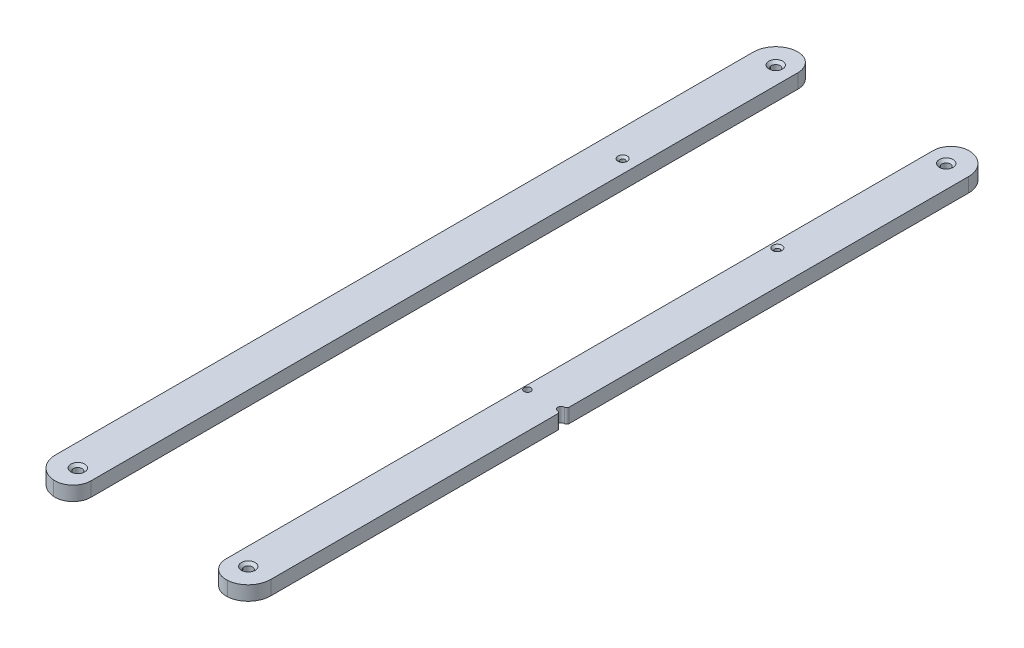
SolidWorks part; units mm, degrees
material "Acrylic (Medium-high impact)"
ref_plane "Front Plane" through (0, 0, 0) normal (0, 0, 1) x (1, 0, 0)
ref_plane "Top Plane" through (0, 0, 0) normal (0, 1, 0) x (1, 0, 0)
ref_plane "Right Plane" through (0, 0, 0) normal (1, 0, 0) x (0, 0, -1)
sketch "Sketch1" plane through (0, 0, 0) normal (0, 1, 0) x (1, 0, 0)
  line L0 (92.5, -137.5) -> (138.3433, -137.5)
  line L1 (148.3433, -127.5) -> (148.3433, 147.5)
  line L2 (158.3433, 157.5) -> (171.8825, 157.5)
  line L3 (181.8825, 167.5) -> (181.8825, 196.879)
  line L4 (171.8825, 206.879) -> (-36.0392, 206.879)
  line L5 (-46.0392, 92.5) -> (-46.0392, 196.879)
  line L6 (-51.0392, 87.5) -> (-77.5, 87.5)
  line L7 (-82.5, 82.5) -> (-82.5, 5)
  line L8 (-77.5, 0) -> (-57.5, 0)
  line L9 (-52.5, -5) -> (-52.5, -162.5)
  line L10 (-47.5, -167.5) -> (72.5, -167.5)
  line L11 (82.5, -157.5) -> (82.5, -147.5)
  line L12 (138.4217, -124.0875) -> (140.4217, -124.0875)
  line L13 (140.4217, -120.9125) -> (138.4217, -120.9125)
  line L14 (138.4217, 23.102) -> (140.4217, 23.102)
  line L15 (140.4217, 26.277) -> (138.4217, 26.277)
  arc A0 (138.3433, -137.5) -> (148.3433, -127.5) centre (138.3433, -127.5) ccw
  arc A1 (158.3433, 157.5) -> (148.3433, 147.5) centre (158.3433, 147.5) ccw
  arc A2 (171.8825, 157.5) -> (181.8825, 167.5) centre (171.8825, 167.5) ccw
  arc A3 (181.8825, 196.879) -> (171.8825, 206.879) centre (171.8825, 196.879) ccw
  arc A4 (-36.0392, 206.879) -> (-46.0392, 196.879) centre (-36.0392, 196.879) ccw
  arc A5 (-51.0392, 87.5) -> (-46.0392, 92.5) centre (-51.0392, 92.5) ccw
  arc A6 (-77.5, 87.5) -> (-82.5, 82.5) centre (-77.5, 82.5) ccw
  arc A7 (-82.5, 5) -> (-77.5, 0) centre (-77.5, 5) ccw
  arc A8 (-52.5, -5) -> (-57.5, 0) centre (-57.5, -5) ccw
  arc A9 (-52.5, -162.5) -> (-47.5, -167.5) centre (-47.5, -162.5) ccw
  arc A10 (72.5, -167.5) -> (82.5, -157.5) centre (72.5, -157.5) ccw
  arc A11 (92.5, -137.5) -> (82.5, -147.5) centre (92.5, -147.5) ccw
  circle A12 centre (67.5, 122.5) radius 1.7
  circle A13 centre (67.5, 82.5) radius 1.7
  circle A14 centre (67.5, 102.5) radius 1.7
  circle A15 centre (37.5, 82.5) radius 1.7
  circle A16 centre (67.5, 147.5) radius 1.7
  circle A17 centre (-32.5, 122.5) radius 1.7
  circle A18 centre (-2.5, 122.5) radius 1.7
  circle A19 centre (37.5, 122.5) radius 1.7
  circle A20 centre (37.5, 102.5) radius 1.7
  circle A21 centre (-32.5, 147.5) radius 1.7
  circle A22 centre (47.4217, 154.379) radius 1.75
  circle A23 centre (47.4217, 146.879) radius 1.5
  circle A24 centre (47.4217, 139.379) radius 1.75
  circle A25 centre (-6.5783, 139.379) radius 1.75
  circle A26 centre (-6.5783, 146.879) radius 1.5
  circle A27 centre (-6.5783, 154.379) radius 1.75
  circle A28 centre (-15.9636, -158.3264) radius 1.4732
  circle A29 centre (44.1717, 16.2044) radius 1.7272
  circle A30 centre (29.1717, 36.5) radius 1.7272
  circle A31 centre (29.1717, 18.5) radius 1.7272
  circle A32 centre (52.0479, 6.6629) radius 1.4732
  circle A33 centre (44.1717, 27.5) radius 1.5
  circle A34 centre (44.1717, 38.7956) radius 1.7272
  circle A35 centre (52.207, 48.3264) radius 1.4732
  circle A36 centre (1.5717, -18.5) radius 1.7272
  circle A37 centre (-13.4283, -16.2044) radius 1.7272
  circle A38 centre (-21.3046, -6.6629) radius 1.4732
  circle A39 centre (-37.0781, 27.5) radius 1.4732
  circle A40 centre (-23.3283, 27.5) radius 1.5
  circle A41 centre (-15.8283, 27.5) radius 1.7272
  circle A42 centre (-0.8283, 36.5) radius 1.7272
  circle A43 centre (-0.8283, 18.5) radius 1.7272
  circle A44 centre (-31.9281, -82.5) radius 1.4732
  circle A45 centre (73.3214, -137.5) radius 1.4732
  circle A46 centre (59.5717, -137.5) radius 1.5
  circle A47 centre (52.0717, -137.5) radius 1.7272
  circle A48 centre (-18.1783, -82.5) radius 1.5
  circle A49 centre (-10.6783, -82.5) radius 1.7272
  circle A50 centre (4.3217, -91.5) radius 1.7272
  circle A51 centre (4.3217, -73.5) radius 1.7272
  circle A52 centre (37.0717, -128.5) radius 1.7272
  circle A53 centre (37.0717, -146.5) radius 1.7272
  circle A54 centre (7.0717, -128.5) radius 1.7272
  circle A55 centre (7.0717, -146.5) radius 1.7272
  circle A56 centre (-15.8046, -116.6629) radius 1.4732
  circle A57 centre (-7.9283, -148.7956) radius 1.7272
  circle A58 centre (-7.9283, -126.2044) radius 1.7272
  circle A59 centre (-7.9283, -137.5) radius 1.5
  circle A60 centre (-21.4636, -48.3264) radius 1.4732
  circle A61 centre (-13.4283, -38.7956) radius 1.7272
  circle A62 centre (1.5717, -36.5) radius 1.7272
  circle A63 centre (-13.4283, -27.5) radius 1.5
  circle A64 centre (31.5717, -18.5) radius 1.7272
  circle A65 centre (31.5717, -36.5) radius 1.7272
  circle A66 centre (46.5717, -27.5) radius 1.7272
  circle A67 centre (54.0717, -27.5) radius 1.5
  circle A68 centre (57.1979, -103.3371) radius 1.4732
  circle A69 centre (49.3217, -93.7956) radius 1.7272
  circle A70 centre (34.3217, -91.5) radius 1.7272
  circle A71 centre (34.3217, -73.5) radius 1.7272
  circle A72 centre (49.3217, -82.5) radius 1.5
  circle A73 centre (49.3217, -71.2044) radius 1.7272
  circle A74 centre (57.357, -61.6736) radius 1.4732
  circle A75 centre (67.8214, -27.5) radius 1.4732
  circle A76 centre (-44.5, -159.5) radius 1.5
  circle A77 centre (74.5, -159.5) radius 1.5
  circle A78 centre (74.5, 159.5) radius 1.5
  circle A79 centre (-38.0392, 159.5) radius 1.5
  circle A80 centre (67.5, 130) radius 2.15
  circle A81 centre (67.5, 65) radius 2.15
  circle A82 centre (67.5, 0) radius 2.15
  circle A83 centre (67.5, -65) radius 2.15
  circle A84 centre (67.5, -130) radius 2.15
  circle A85 centre (-32.5, -130) radius 2.15
  circle A86 centre (-32.5, -65) radius 2.15
  circle A87 centre (-32.5, 65) radius 2.15
  circle A88 centre (-32.5, 130) radius 2.15
  circle A89 centre (22.0717, -137.5) radius 13
  circle A90 centre (19.3217, -82.5) radius 13
  circle A91 centre (16.5717, -27.5) radius 13
  circle A92 centre (14.1717, 27.5) radius 13
  circle A93 centre (-32.5, 0) radius 2.15
  arc A94 (140.4217, -124.0875) -> (140.4217, -120.9125) centre (140.4217, -122.5) ccw
  arc A95 (138.4217, -120.9125) -> (138.4217, -124.0875) centre (138.4217, -122.5) ccw
  arc A96 (140.4217, 23.102) -> (140.4217, 26.277) centre (140.4217, 24.6895) ccw
  arc A97 (138.4217, 26.277) -> (138.4217, 23.102) centre (138.4217, 24.6895) ccw
  circle A98 centre (90.4217, -122.5) radius 1.5875
  circle A99 centre (90.4217, 24.6895) radius 1.5875
  circle A100 centre (97.9217, 186.879) radius 1.5875
  circle A101 centre (67.9217, 186.879) radius 1.5875
  circle A102 centre (37.9217, 186.879) radius 1.5875
  circle A103 centre (148.1417, 186.879) radius 4.7625
  circle A104 centre (-12.2983, 186.879) radius 4.7625
  text T0 "SOLIDWORKS Educational Product." font "SWTXT" height 4.8336
  text T1 "For Instructional Use Only." font "SWTXT" height 4.8336
sketch "Sketch2" plane through (0, 0, 0) normal (0, 1, 0) x (1, 0, 0)
  line L0 (0, 0) -> (-75, 0) construction
  line L1 (-75, -165) -> (75, -165)
  line L2 (-75, -165) -> (-75, 165)
  line L3 (-75, 165) -> (75, 165)
  line L4 (75, -165) -> (75, 165)
  line L5 (-75, -165) -> (75, 165) construction
  line L6 (-75, 165) -> (75, -165) construction
  circle A0 centre (-50, 129.505) radius 2
  circle A1 centre (50, 129.505) radius 2
  circle A2 centre (50, 64.505) radius 2
  circle A3 centre (-50, 64.505) radius 2
  circle A9 centre (50, -129.505) radius 2
  circle A10 centre (-50, -129.505) radius 2
  circle A11 centre (-50, -64.505) radius 2
  circle A12 centre (50, -64.505) radius 2
  point P0 (0, 0)
  dimension "D5" = 4
  dimension "D1" = 150
  dimension "D2" = 330
  dimension "D3" = 50
  dimension "D4" = 129.505
  dimension "D6" = 2
  dimension "D7" = 2
extrude "Boss-Extrude1" add sketch "Sketch2" along normal blind 6.35
sketch "Sketch4" plane through (0, 6.35, 0) normal (0, 1, 0) x (1, 0, 0)
  circle A0 centre (1.85, -25) radius 7
  circle A1 centre (-1.15, 25) radius 7
  circle A2 centre (-4.15, 75) radius 7
  circle A3 centre (-7.15, 125) radius 7
  circle A4 centre (13, -70) radius 1.5
  circle A5 centre (16, -90) radius 1.5
  circle A6 centre (19, -110) radius 1.5
  circle A7 centre (22, -130) radius 1.5
  dimension "D8" = 14
  dimension "D9" = 14
  dimension "D10" = 14
  dimension "D11" = 14
  dimension "D16" = 3
  dimension "D1" = 25
  dimension "D2" = 50
  dimension "D3" = 3
  dimension "D4" = 3
  dimension "D5" = 3
  dimension "D6" = 50
  dimension "D7" = 50
  dimension "D12" = 1.85
  dimension "D17" = 3
  dimension "D18" = 3
  dimension "D19" = 3
  dimension "D20" = 70
  dimension "D21" = 20
  dimension "D22" = 20
  dimension "D23" = 20
  dimension "D24" = 13
extrude "Cut-Extrude1" cut sketch "Sketch4" against normal through all
sketch "Sketch6" plane through (0, 6.35, 0) normal (0, 1, 0) x (1, 0, 0)
  circle A0 centre (13, -70) radius 8
  circle A1 centre (16, -90) radius 8
  circle A2 centre (19, -110) radius 8
  circle A3 centre (22, -130) radius 8
  circle A4 centre (31.85, -25) radius 5
  circle A5 centre (46.85, -25) radius 5
  circle A6 centre (61.85, -25) radius 5
  circle A7 centre (1.85, -25) radius 7 construction
  dimension "D1" = 16
  dimension "D2" = 16
  dimension "D3" = 16
  dimension "D4" = 16
  dimension "D5" = 10
  dimension "D6" = 10
  dimension "D7" = 10
  dimension "D8" = 30
  dimension "D9" = 45
  dimension "D10" = 60
  dimension "D11" = 0
  dimension "D12" = 0
  dimension "D13" = 0
sketch "Sketch7" plane through (0, 6.35, 0) normal (0, 1, 0) x (1, 0, 0)
  circle A0 centre (31.85, -25) radius 1.5
  circle A1 centre (46.85, -25) radius 1.5
  circle A2 centre (61.85, -25) radius 1.5
  dimension "D1" = 3
extrude "Cut-Extrude2" cut sketch "Sketch7" against normal blind 10
sketch "Sketch8" plane through (0, 6.35, 0) normal (0, 1, 0) x (1, 0, 0)
  line L0 (75, 165) -> (-75, 165) construction
  line L1 (-56.35, -165) -> (56.35, -165)
  line L2 (-56.35, -165) -> (-56.35, 165)
  line L3 (-56.35, 165) -> (56.35, 165)
  line L4 (56.35, -165) -> (56.35, 165)
  line L5 (-56.35, -165) -> (56.35, 165) construction
  line L6 (-56.35, 165) -> (56.35, -165) construction
  line L7 (75, -165) -> (75, 165) construction
  line L8 (18.7, -42.5) -> (75, -42.5)
  line L9 (18.7, -42.5) -> (18.7, -7.5)
  line L10 (18.7, -7.5) -> (75, -7.5)
  line L11 (75, -42.5) -> (75, -7.5)
  line L12 (18.7, -42.5) -> (75, -7.5) construction
  line L13 (18.7, -7.5) -> (75, -42.5) construction
  point P0 (0, 0)
  point P8 (46.85, -25)
  circle M2 centre (31.85, -25) radius 1.5
  circle M3 centre (46.85, -25) radius 1.5
  circle M4 centre (61.85, -25) radius 1.5
  circle M5 centre (22, -130) radius 1.5
  circle M6 centre (19, -110) radius 1.5
  circle M7 centre (16, -90) radius 1.5
  circle M8 centre (-1.15, 25) radius 7
  circle M9 centre (-4.15, 75) radius 7
  circle M10 centre (-7.15, 125) radius 7
  circle M11 centre (13, -70) radius 1.5
  circle M12 centre (1.85, -25) radius 7
  line M13 (75, -165) -> (75, 165)
  line M14 (75, 165) -> (-75, 165)
  line M16 (-75, -165) -> (75, -165)
  circle M17 centre (-50, 129.505) radius 2
  circle M18 centre (50, 129.505) radius 2
  circle M19 centre (50, 64.505) radius 2
  circle M20 centre (-50, 64.505) radius 2
  circle M21 centre (50, -129.505) radius 2
  circle M22 centre (-50, -129.505) radius 2
  circle M23 centre (-50, -64.505) radius 2
  circle M24 centre (50, -64.505) radius 2
  dimension "D1" = 112.7
  dimension "D2" = 35
extrude "Cut-Extrude3" cut sketch "Sketch8" against normal blind 10 flip side to cut contours L10 L4 L8 M13 M3 M4 | L9 L10 L4 L2 L8 M14 M16 M5 M7 M9 M11 M18 M20 M22 M24 M23 M21 M19 M17 M12 M10 M8 M6 | L10 L9 L8 L4 M2
hole_wizard "CSK for #10 Flat Head Machine Screw (100)1" [suppressed] positions "Sketch33" profile "Sketch34" countersink size "#10" standard "ANSI Inch"
sketch "Sketch33" plane through (0, 6.35, 0) normal (0, 1, 0) x (1, 0, 0)
  line L0 (0, -3.4925) -> (0, 3.4925) construction
  line L1 (-3.4925, 0) -> (3.4925, 0) construction
  point P0 (-37.85, -155)
  point P7 (37.85, -155)
  point P10 (37.85, 155)
  point P11 (-37.85, 155)
sketch "Sketch34" plane through (-37.85, 6.35, 155) normal (1, 0, 0) x (0, 0, 1)
  line L0 (0, 0) -> (0, 6.35)
  line L1 (0, 6.35) -> (2.5527, 6.35)
  line L2 (2.5527, 6.35) -> (2.5527, 1.9608)
  line L3 (2.5527, 1.9608) -> (4.8895, 0)
  line L5 (4.8895, 0) -> (0, 0)
  line L6 (-2.5527, 1.9608) -> (-4.8895, 0) construction
  line L11 (0, -6.35) -> (0, 107.95) construction
  dimension "Thru Hole Dia." = 5.1054
  dimension "Thru Hole Depth" = 6.35
  dimension "Near C'Sink Dia." = 9.779
  dimension "Near C'Sink Angle" = 100
fillet "Fillet2" radius 8 8 edges at (-56.35, 3.175, 165) (56.35, 3.175, 165) (-56.35, 3.175, -165) (56.35, 3.175, -165) (56.35, 3.175, 7.5) (75, 3.175, 7.5) (56.35, 3.175, 42.5) (75, 3.175, 42.5)
sketch "Sketch15" plane through (0, 6.35, 0) normal (0, 1, 0) x (1, 0, 0)
  line L0 (-50, -134.505) -> (-50, -124.505) construction
  line L1 (-52, -134.505) -> (-52, -124.505)
  line L2 (-48, -134.505) -> (-48, -124.505)
  line L3 (50, -134.505) -> (50, -124.505) construction
  line L4 (48, -134.505) -> (48, -124.505)
  line L5 (52, -134.505) -> (52, -124.505)
  line L6 (50, -69.505) -> (50, -59.505) construction
  line L7 (48, -69.505) -> (48, -59.505)
  line L8 (52, -69.505) -> (52, -59.505)
  line L9 (-50, -69.505) -> (-50, -59.505) construction
  line L10 (-52, -69.505) -> (-52, -59.505)
  line L11 (-48, -69.505) -> (-48, -59.505)
  line L12 (0, 0) -> (-81.6397, 0) construction
  line L13 (-50, 134.505) -> (-50, 124.505) construction
  line L14 (-52, 134.505) -> (-52, 124.505)
  line L15 (-48, 134.505) -> (-48, 124.505)
  line L16 (50, 134.505) -> (50, 124.505) construction
  line L17 (48, 134.505) -> (48, 124.505)
  line L18 (52, 134.505) -> (52, 124.505)
  line L19 (50, 69.505) -> (50, 59.505) construction
  line L20 (48, 69.505) -> (48, 59.505)
  line L21 (52, 69.505) -> (52, 59.505)
  line L22 (-50, 69.505) -> (-50, 59.505) construction
  line L23 (-52, 69.505) -> (-52, 59.505)
  line L24 (-48, 69.505) -> (-48, 59.505)
  arc A0 (-52, -134.505) -> (-48, -134.505) centre (-50, -134.505) ccw
  arc A1 (-48, -124.505) -> (-52, -124.505) centre (-50, -124.505) ccw
  circle A2 centre (-50, -129.505) radius 2 construction
  arc A3 (48, -134.505) -> (52, -134.505) centre (50, -134.505) ccw
  arc A4 (52, -124.505) -> (48, -124.505) centre (50, -124.505) ccw
  arc A5 (48, -69.505) -> (52, -69.505) centre (50, -69.505) ccw
  arc A6 (52, -59.505) -> (48, -59.505) centre (50, -59.505) ccw
  arc A7 (-52, -69.505) -> (-48, -69.505) centre (-50, -69.505) ccw
  arc A8 (-48, -59.505) -> (-52, -59.505) centre (-50, -59.505) ccw
  arc A9 (-52, 134.505) -> (-48, 134.505) centre (-50, 134.505) cw
  arc A10 (-48, 124.505) -> (-52, 124.505) centre (-50, 124.505) cw
  arc A11 (48, 134.505) -> (52, 134.505) centre (50, 134.505) cw
  arc A12 (52, 124.505) -> (48, 124.505) centre (50, 124.505) cw
  arc A13 (48, 69.505) -> (52, 69.505) centre (50, 69.505) cw
  arc A14 (52, 59.505) -> (48, 59.505) centre (50, 59.505) cw
  arc A15 (-52, 69.505) -> (-48, 69.505) centre (-50, 69.505) cw
  arc A16 (-48, 59.505) -> (-52, 59.505) centre (-50, 59.505) cw
  point P2 (-50, -129.505)
  point P14 (50, -129.505)
  point P21 (50, -64.505)
  point P28 (-50, -64.505)
  point P35 (-50, 129.505)
  point P42 (50, 129.505)
  point P49 (50, 64.505)
  point P56 (-50, 64.505)
  dimension "D1" = 10
  dimension "D2" = 2
  dimension "D3" = 2
extrude "Cut-Extrude7" cut sketch "Sketch15" against normal blind 10
sketch "Sketch20" plane through (0, 6.35, 0) normal (0, 1, 0) x (1, 0, 0)
  line L0 (0, 0) -> (-103.422, 0) construction
  line L1 (0, 0) -> (0, -165) construction
  line L2 (-48.35, -165) -> (48.35, -165) construction
  circle A0 centre (-50, -144.505) radius 1.5
  circle A1 centre (-50, -79.505) radius 1.5
  arc A2 (-48, -59.505) -> (-52, -59.505) centre (-50, -59.505) ccw construction
  arc A3 (-52, -134.505) -> (-48, -134.505) centre (-50, -134.505) ccw construction
  circle A4 centre (50, -79.505) radius 1.5
  circle A5 centre (50, -144.505) radius 1.5
  circle A6 centre (50, 144.505) radius 1.5
  circle A7 centre (50, 79.505) radius 1.5
  circle A8 centre (-50, 79.505) radius 1.5
  circle A9 centre (-50, 144.505) radius 1.5
  dimension "D1" = 3
  dimension "D2" = 3
  dimension "D4" = 10
  dimension "D3" = 20
extrude "Cut-Extrude12" cut sketch "Sketch20" against normal blind 36.83
sketch "Sketch18" plane through (0, 6.35, 0) normal (0, 1, 0) x (1, 0, 0)
  line L0 (1.85, -25) -> (-1.15, 25) construction
  line L1 (1.85, -25) -> (-7.15, 125) construction
  line L2 (1.85, -25) -> (19.9658, -23.9131) construction
  line L3 (0, 0) -> (-23.1008, -1.386) construction
  line L4 (1.85, -25) -> (1.85, 25) construction
  line L5 (1.85, 25) -> (-1.15, 25) construction
  line L6 (-10.65, -33.5) -> (-21.8318, 152.8626) construction
  line L7 (-10.65, -4.5) -> (-20.597, 161.283) construction
  circle A0 centre (14.35, -33.5) radius 1.35
  circle A1 centre (-10.65, -33.5) radius 1.35
  circle A2 centre (14.35, -4.5) radius 1.35
  circle A4 centre (-10.65, -4.5) radius 1.35
  circle A5 centre (-13.65, 16.5) radius 1.35
  circle A6 centre (-13.65, 45.5) radius 1.35
  circle A7 centre (-16.65, 66.5) radius 1.35
  circle A8 centre (-16.65, 95.5) radius 1.35
  circle A9 centre (-19.65, 116.5) radius 1.35
  circle A10 centre (-19.65, 145.5) radius 1.35
  dimension "D1" = 2.7
  dimension "D2" = 2.7
  dimension "D3" = 2.7
  dimension "D7" = 3.434
  dimension "D10" = 2.7
  dimension "D11" = 2.7
  dimension "D17" = 2.7
  dimension "D18" = 2.7
  dimension "D19" = 2.7
  dimension "D20" = 2.7
  dimension "D21" = 2.7
  dimension "D4" = 29
  dimension "D5" = 25
  dimension "D6" = 8.5
  dimension "D8" = 50
  dimension "D9" = 50
  dimension "D12" = 0
  dimension "D13" = 50
  dimension "D14" = 50
  dimension "D15" = 50
  dimension "D16" = 50
  dimension "D22" = 25
extrude "Cut-Extrude10" cut sketch "Sketch18" against normal blind 36.83
sketch "Sketch19" plane through (0, 6.35, 0) normal (0, 1, 0) x (1, 0, 0)
  line L0 (-10.65, -33.5) -> (-10.65, -18.5) construction
  line L1 (-12, -33.5) -> (-12, -18.5)
  line L2 (-9.3, -33.5) -> (-9.3, -18.5)
  line L3 (-10.65, -4.5) -> (-10.65, 10.5) construction
  line L4 (-12, -4.5) -> (-12, 10.5)
  line L5 (-9.3, -4.5) -> (-9.3, 10.5)
  line L6 (-13.65, 16.5) -> (-13.65, 31.5) construction
  line L7 (-15, 16.5) -> (-15, 31.5)
  line L8 (-12.3, 16.5) -> (-12.3, 31.5)
  line L9 (-13.65, 45.5) -> (-13.65, 60.5) construction
  line L10 (-15, 45.5) -> (-15, 60.5)
  line L11 (-12.3, 45.5) -> (-12.3, 60.5)
  line L12 (-16.65, 66.5) -> (-16.65, 81.5) construction
  line L13 (-18, 66.5) -> (-18, 81.5)
  line L14 (-15.3, 66.5) -> (-15.3, 81.5)
  line L15 (-16.65, 95.5) -> (-16.65, 110.5) construction
  line L16 (-18, 95.5) -> (-18, 110.5)
  line L17 (-15.3, 95.5) -> (-15.3, 110.5)
  line L18 (-19.65, 116.5) -> (-19.65, 131.5) construction
  line L19 (-21, 116.5) -> (-21, 131.5)
  line L20 (-18.3, 116.5) -> (-18.3, 131.5)
  line L21 (-19.65, 145.5) -> (-19.65, 160.5) construction
  line L22 (-21, 145.5) -> (-21, 160.5)
  line L23 (-18.3, 145.5) -> (-18.3, 160.5)
  line L24 (1.85, -25) -> (1.85, 0) construction
  line L25 (-1.15, 18) -> (-1.15, 48.7099) construction
  line L26 (-4.15, 68) -> (-4.15, 93.5922) construction
  line L27 (-7.15, 118) -> (-7.15, 145.5) construction
  line L28 (14.35, -4.5) -> (14.35, 10.5) construction
  line L29 (15.7, -4.5) -> (15.7, 10.5)
  line L30 (13, -4.5) -> (13, 10.5)
  line L31 (14.35, -33.5) -> (14.35, -18.5) construction
  line L32 (15.7, -33.5) -> (15.7, -18.5)
  line L33 (13, -33.5) -> (13, -18.5)
  line L34 (11.35, 45.5) -> (11.35, 60.5) construction
  line L35 (12.7, 45.5) -> (12.7, 60.5)
  line L36 (10, 45.5) -> (10, 60.5)
  line L37 (11.35, 16.5) -> (11.35, 31.5) construction
  line L38 (12.7, 16.5) -> (12.7, 31.5)
  line L39 (10, 16.5) -> (10, 31.5)
  line L40 (8.35, 95.5) -> (8.35, 110.5) construction
  line L41 (9.7, 95.5) -> (9.7, 110.5)
  line L42 (7, 95.5) -> (7, 110.5)
  line L43 (8.35, 66.5) -> (8.35, 81.5) construction
  line L44 (9.7, 66.5) -> (9.7, 81.5)
  line L45 (7, 66.5) -> (7, 81.5)
  line L46 (5.35, 145.5) -> (5.35, 160.5) construction
  line L47 (6.7, 145.5) -> (6.7, 160.5)
  line L48 (4, 145.5) -> (4, 160.5)
  line L49 (5.35, 116.5) -> (5.35, 131.5) construction
  line L50 (6.7, 116.5) -> (6.7, 131.5)
  line L51 (4, 116.5) -> (4, 131.5)
  line L52 (1.85, -25) -> (1.85, -10) construction
  line L53 (-5.15, -25) -> (-5.15, -10)
  line L54 (8.85, -25) -> (8.85, -10)
  line L55 (-1.15, 25) -> (-1.15, 40) construction
  line L56 (-8.15, 25) -> (-8.15, 40)
  line L57 (5.85, 25) -> (5.85, 40)
  line L58 (-4.15, 75) -> (-4.15, 89) construction
  line L59 (-11.15, 75) -> (-11.15, 89)
  line L60 (2.85, 75) -> (2.85, 89)
  line L61 (-7.15, 125) -> (-7.15, 139) construction
  line L62 (-14.15, 125) -> (-14.15, 139)
  line L63 (-0.15, 125) -> (-0.15, 139)
  arc A0 (-12, -33.5) -> (-9.3, -33.5) centre (-10.65, -33.5) ccw
  arc A1 (-9.3, -18.5) -> (-12, -18.5) centre (-10.65, -18.5) ccw
  arc A2 (-12, -4.5) -> (-9.3, -4.5) centre (-10.65, -4.5) ccw
  arc A3 (-9.3, 10.5) -> (-12, 10.5) centre (-10.65, 10.5) ccw
  arc A4 (-15, 16.5) -> (-12.3, 16.5) centre (-13.65, 16.5) ccw
  arc A5 (-12.3, 31.5) -> (-15, 31.5) centre (-13.65, 31.5) ccw
  arc A6 (-15, 45.5) -> (-12.3, 45.5) centre (-13.65, 45.5) ccw
  arc A7 (-12.3, 60.5) -> (-15, 60.5) centre (-13.65, 60.5) ccw
  arc A8 (-18, 66.5) -> (-15.3, 66.5) centre (-16.65, 66.5) ccw
  arc A9 (-15.3, 81.5) -> (-18, 81.5) centre (-16.65, 81.5) ccw
  arc A10 (-18, 95.5) -> (-15.3, 95.5) centre (-16.65, 95.5) ccw
  arc A11 (-15.3, 110.5) -> (-18, 110.5) centre (-16.65, 110.5) ccw
  arc A12 (-21, 116.5) -> (-18.3, 116.5) centre (-19.65, 116.5) ccw
  arc A13 (-18.3, 131.5) -> (-21, 131.5) centre (-19.65, 131.5) ccw
  arc A14 (-21, 145.5) -> (-18.3, 145.5) centre (-19.65, 145.5) ccw
  arc A15 (-18.3, 160.5) -> (-21, 160.5) centre (-19.65, 160.5) ccw
  circle A16 centre (-1.15, 25) radius 7 construction
  circle A17 centre (-4.15, 75) radius 7 construction
  circle A18 centre (-7.15, 125) radius 7 construction
  arc A19 (15.7, -4.5) -> (13, -4.5) centre (14.35, -4.5) cw
  arc A20 (13, 10.5) -> (15.7, 10.5) centre (14.35, 10.5) cw
  arc A21 (15.7, -33.5) -> (13, -33.5) centre (14.35, -33.5) cw
  arc A22 (13, -18.5) -> (15.7, -18.5) centre (14.35, -18.5) cw
  arc A23 (12.7, 45.5) -> (10, 45.5) centre (11.35, 45.5) cw
  arc A24 (10, 60.5) -> (12.7, 60.5) centre (11.35, 60.5) cw
  arc A25 (12.7, 16.5) -> (10, 16.5) centre (11.35, 16.5) cw
  arc A26 (10, 31.5) -> (12.7, 31.5) centre (11.35, 31.5) cw
  arc A27 (9.7, 95.5) -> (7, 95.5) centre (8.35, 95.5) cw
  arc A28 (7, 110.5) -> (9.7, 110.5) centre (8.35, 110.5) cw
  arc A29 (9.7, 66.5) -> (7, 66.5) centre (8.35, 66.5) cw
  arc A30 (7, 81.5) -> (9.7, 81.5) centre (8.35, 81.5) cw
  arc A31 (6.7, 145.5) -> (4, 145.5) centre (5.35, 145.5) cw
  arc A32 (4, 160.5) -> (6.7, 160.5) centre (5.35, 160.5) cw
  arc A33 (6.7, 116.5) -> (4, 116.5) centre (5.35, 116.5) cw
  arc A34 (4, 131.5) -> (6.7, 131.5) centre (5.35, 131.5) cw
  arc A35 (-5.15, -25) -> (8.85, -25) centre (1.85, -25) ccw
  arc A36 (8.85, -10) -> (-5.15, -10) centre (1.85, -10) ccw
  arc A37 (-8.15, 25) -> (5.85, 25) centre (-1.15, 25) ccw
  arc A38 (5.85, 40) -> (-8.15, 40) centre (-1.15, 40) ccw
  arc A39 (-11.15, 75) -> (2.85, 75) centre (-4.15, 75) ccw
  arc A40 (2.85, 89) -> (-11.15, 89) centre (-4.15, 89) ccw
  arc A41 (-14.15, 125) -> (-0.15, 125) centre (-7.15, 125) ccw
  arc A42 (-0.15, 139) -> (-14.15, 139) centre (-7.15, 139) ccw
  point P3 (-10.65, -26)
  point P8 (-10.65, 3)
  point P16 (-13.65, 24)
  point P24 (-13.65, 53)
  point P32 (-16.65, 74)
  point P40 (-16.65, 103)
  point P48 (-19.65, 124)
  point P56 (-19.65, 153)
  point P83 (14.35, 3)
  point P90 (14.35, -26)
  point P97 (11.35, 53)
  point P104 (11.35, 24)
  point P111 (8.35, 103)
  point P118 (8.35, 74)
  point P125 (5.35, 153)
  point P132 (5.35, 124)
  point P137 (1.85, -17.5)
  point P145 (-1.15, 32.5)
  point P151 (-4.15, 82)
  point P158 (-7.15, 132)
  dimension "D1" = 1.35
  dimension "D2" = 1.35
  dimension "D3" = 1.35
  dimension "D4" = 1.35
  dimension "D5" = 1.35
  dimension "D6" = 1.35
  dimension "D7" = 1.35
  dimension "D8" = 1.35
  dimension "D17" = 7
  dimension "D19" = 7
  dimension "D21" = 7
  dimension "D23" = 7
  dimension "D9" = 15
  dimension "D10" = 15
  dimension "D11" = 15
  dimension "D12" = 15
  dimension "D13" = 15
  dimension "D14" = 15
  dimension "D15" = 15
  dimension "D16" = 15
  dimension "D18" = 15
  dimension "D20" = 15
  dimension "D22" = 14
  dimension "D24" = 14
extrude "Cut-Extrude11" cut sketch "Sketch19" against normal blind 36.83
sketch "Sketch10" [suppressed] plane through (0, 3.175, 0) normal (0, 1, 0) x (1, 0, 0)
  line L1 (26.35, 5) -> (-37.65, 5)
  line L2 (26.35, 5) -> (26.35, 160)
  line L3 (26.35, 160) -> (-37.65, 160)
  line L4 (-37.65, 5) -> (-37.65, 160)
  circle A0 centre (1.35, 30) radius 12.5 construction
  circle A1 centre (-7.65, 135) radius 12.5 construction
  dimension "D1" = 25
  dimension "D2" = 30
  dimension "D3" = 25
  dimension "D4" = 25
extrude "Cut-Extrude5" [suppressed] cut sketch "Sketch10" against normal blind 10 flip side to cut
sketch "Sketch11" [suppressed] plane through (0, 3.175, 0) normal (0, 1, 0) x (1, 0, 0)
  circle A0 centre (1.35, 30) radius 12.5
  circle A1 centre (1.35, 30) radius 7.825
  circle A2 centre (-1.65, 65) radius 12.5
  circle A3 centre (-1.65, 65) radius 7.825
  circle A4 centre (-4.65, 100) radius 7.825
  circle A5 centre (-4.65, 100) radius 12.5
  circle A6 centre (-7.65, 135) radius 12.5
  circle A7 centre (-7.65, 135) radius 7.825
  dimension "D1" = 15.65
  dimension "D2" = 15.65
  dimension "D3" = 15.65
  dimension "D4" = 15.65
extrude "Boss-Extrude2" [suppressed] add sketch "Sketch11" against normal up to surface (3.175 mm away)
fillet "Fillet3" [suppressed] radius 10
sketch "Sketch16" [suppressed] plane through (0, 3.175, 0) normal (0, 1, 0) x (1, 0, 0)
  line L1 (32.1645, -80.682) -> (14.5365, -80.682)
  line L2 (32.1645, -80.682) -> (32.1645, -6.78)
  line L3 (32.1645, -6.78) -> (14.5365, -6.78)
  line L4 (14.5365, -80.682) -> (14.5365, -6.78)
  line L5 (32.1645, -80.682) -> (14.5365, -6.78) construction
  line L6 (32.1645, -6.78) -> (14.5365, -80.682) construction
  line L7 (86.4675, 24.1346) -> (36.2325, 24.1346)
  line L8 (86.4675, 24.1346) -> (86.4675, 38.646)
  line L9 (86.4675, 38.646) -> (36.2325, 38.646)
  line L10 (36.2325, 24.1346) -> (36.2325, 38.646)
  line L11 (86.4675, 24.1346) -> (36.2325, 38.646) construction
  line L12 (86.4675, 38.646) -> (36.2325, 24.1346) construction
  circle A0 centre (61.35, 29.8903) radius 1.5 construction
  point P0 (23.3505, -43.731)
  point P5 (61.35, 31.3903)
extrude "Boss-Extrude5" [suppressed] add sketch "Sketch16" against normal up to surface (3.175 mm away)
sketch "Sketch17" [suppressed] plane through (0, 6.35, 0) normal (0, 1, 0) x (1, 0, 0)
  line L1 (-48.35, -165) -> (48.35, -165) construction
  line L2 (42, -165) -> (-42, -165)
  line L3 (-42, -165) -> (-42, -51.505)
  line L4 (-42, -51.505) -> (-56.35, -51.505)
  line L5 (-56.35, -157) -> (-56.35, 157) construction
  line L6 (-56.35, -51.505) -> (-56.35, 51.505)
  line L8 (0, -165) -> (0, 165) construction
  line L9 (0, 0) -> (-56.35, 0) construction
  line L10 (42, -51.505) -> (56.35, -51.505)
  line L12 (42, -165) -> (42, -51.505)
  line L13 (42, 165) -> (42, 51.505)
  line L14 (42, 51.505) -> (56.35, 51.505)
  line L15 (-42, 51.505) -> (-56.35, 51.505)
  line L16 (-42, 165) -> (-42, 51.505)
  line L17 (42, 165) -> (-42, 165)
  line L18 (56.35, -51.505) -> (87.4758, -51.505)
  line L19 (27, -135) -> (8, -135)
  line L20 (27, -135) -> (27, -65)
  line L21 (27, -65) -> (8, -65)
  line L22 (8, -135) -> (8, -65)
  line L23 (26.85, -30) -> (66.85, -30)
  line L24 (26.85, -30) -> (26.85, -20)
  line L25 (26.85, -20) -> (66.85, -20)
  line L26 (66.85, -30) -> (66.85, -20)
  line L27 (87.4758, -51.505) -> (87.4758, 51.505)
  line L28 (87.4758, 51.505) -> (56.35, 51.505)
  arc A0 (-52, -134.505) -> (-48, -134.505) centre (-50, -134.505) ccw construction
  arc A1 (-48, -59.505) -> (-52, -59.505) centre (-50, -59.505) ccw construction
  circle A2 centre (22, -130) radius 1.5 construction
  circle A3 centre (13, -70) radius 1.5 construction
  circle A4 centre (31.85, -25) radius 1.5 construction
  circle A5 centre (61.85, -25) radius 1.5 construction
  point P15 (-50, -136.505)
  point P27 (56.35, 0)
  dimension "D5" = 5
  dimension "D1" = 8
  dimension "D2" = 8
  dimension "D3" = 5
  dimension "D4" = 5
  dimension "D6" = 5
  dimension "D7" = 5
  dimension "D8" = 5
  dimension "D9" = 5
  dimension "D10" = 5
extrude "Cut-Extrude9" [suppressed] cut sketch "Sketch17" against normal blind 10 contours L14 L13 L17 L16 L15 L6 L4 L3 L2 L12 L10 L18 L27 L28 | L20 L19 L22 L21 | L24 L23 L26 L25
fillet "Fillet5" [suppressed] radius 5
fillet "Fillet6" [suppressed] radius 5
fillet "Fillet7" [suppressed] radius 5
fillet "Fillet8" [suppressed] radius 5
fillet "Fillet9" [suppressed] radius 5
fillet "Fillet10" [suppressed] radius 5
sketch "Sketch21" plane through (0, 6.35, 0) normal (0, 1, 0) x (1, 0, 0)
  line L0 (-48.35, -165) -> (48.35, -165) construction
  line L1 (47.85, -165) -> (-47.85, -165)
  line L2 (47.85, -165) -> (47.85, 165)
  line L3 (47.85, 165) -> (-47.85, 165)
  line L4 (-47.85, -165) -> (-47.85, 165)
  line L5 (48.35, 165) -> (-48.35, 165) construction
  line L6 (-56.35, -157) -> (-56.35, 157) construction
  line L7 (56.35, -157) -> (56.35, -50.5) construction
  dimension "D1" = 8.5
  dimension "D2" = 8.5
extrude "Cut-Extrude13" cut sketch "Sketch21" against normal through all flip side to cut
sketch "Sketch23" plane through (0, 6.35, 0) normal (0, 1, 0) x (1, 0, 0)
  line L0 (-47.85, -165) -> (47.85, -165) construction
  line L1 (47.85, -23.882) -> (47.85, 165) construction
  line L2 (-47.85, 165) -> (-47.85, -165) construction
  line L3 (-47.85, -165) -> (47.85, -165) construction
  point P0 (0, -145)
  point P1 (0, -105)
  point P2 (-35.85, 85)
  point P3 (0, -65)
  point P6 (32.85, 85)
  dimension "D1" = 20
  dimension "D2" = 100
  dimension "D3" = 40
  dimension "D4" = 15
  dimension "D5" = 12
  dimension "D6" = 250
  dimension "D7" = 250
hole_wizard "#4-40 Tapped Hole1" positions "Sketch31" profile "Sketch32" tap size "#4-40" standard "ANSI Inch"
sketch "Sketch31" [suppressed] plane through (0, 6.35, 0) normal (0, 1, 0) x (1, 0, 0)
  point P0 (-35.85, 85)
  point P3 (32.85, 85)
sketch "Sketch32" plane through (-35.85, 6.35, -85) normal (1, 0, 0) x (0, 0, 1)
  line L0 (0, 0) -> (0, 6.35)
  line L1 (0, 6.35) -> (1.1303, 6.35)
  line L2 (1.1303, 6.35) -> (1.1303, 0.9271)
  line L3 (1.1303, 0.9271) -> (2.0574, 0)
  line L5 (2.0574, 0) -> (0, 0)
  line L6 (-1.1303, 0.9271) -> (-2.0574, 0) construction
  line L11 (0, -6.35) -> (0, 107.95) construction
  dimension "Thru Tap Drill Dia." = 2.2606
  dimension "Thru Tap Drill Depth" = 6.35
  dimension "Near C'Sink Dia." = 4.1148
  dimension "Near C'Sink Angle" = 90
cosmetic thread "Hole Thread10" parameters "D2"=2.8448
cosmetic thread "Hole Thread11" parameters "D2"=2.8448
hole_wizard "#4-40 Tapped Hole2" positions "Sketch24" profile "Sketch26" tap size "#4-40" standard "ANSI Inch"
sketch "Sketch24" [suppressed] plane through (0, 6.35, 0) normal (0, 1, 0) x (1, 0, 0)
  point P0 (0, -145)
  point P3 (0, -65)
  point P6 (0, -105)
sketch "Sketch26" plane through (0, 6.35, 145) normal (1, 0, 0) x (0, 0, 1)
  line L0 (0, 0) -> (0, 6.35)
  line L1 (0, 6.35) -> (1.1303, 6.35)
  line L2 (1.1303, 6.35) -> (1.1303, 0.9271)
  line L3 (1.1303, 0.9271) -> (2.0574, 0)
  line L5 (2.0574, 0) -> (0, 0)
  line L6 (-1.1303, 0.9271) -> (-2.0574, 0) construction
  line L11 (0, -6.35) -> (0, 107.95) construction
  dimension "Thru Tap Drill Dia." = 2.2606
  dimension "Thru Tap Drill Depth" = 6.35
  dimension "Near C'Sink Dia." = 4.1148
  dimension "Near C'Sink Angle" = 90
cosmetic thread "Hole Thread3" parameters "D2"=2.8448
cosmetic thread "Hole Thread4" parameters "D2"=2.8448
cosmetic thread "Hole Thread5" parameters "D2"=2.8448
fillet "Fillet11" radius 10 4 edges at (-47.85, 3.175, -165) (47.85, 3.175, 165) (47.85, 3.175, -165) (-47.85, 3.175, 165)
sketch "Sketch22" [suppressed] plane through (0, 6.35, 0) normal (0, 1, 0) x (1, 0, 0)
  line L0 (-47.85, -165) -> (47.85, -165) construction
  line L1 (42.85, -165) -> (-42.85, -165)
  line L2 (42.85, -165) -> (42.85, -41.5)
  line L4 (-42.85, -165) -> (-42.85, -41.5)
  line L5 (-42.85, -41.5) -> (-42.85, 145)
  line L6 (-47.85, 165) -> (-47.85, -165) construction
  line L7 (47.85, -165) -> (47.85, -26.118) construction
  line L8 (42.85, -41.5) -> (-42.85, -41.5)
  line L9 (-42.85, 145) -> (-29, 145)
  line L10 (-29, 145) -> (-29, -41.5)
  line L11 (42.85, -41.5) -> (42.85, 145)
  line L12 (42.85, 145) -> (23.7, 145)
  line L13 (23.7, 145) -> (23.7, -41.5)
  line L14 (15.7, -33.5) -> (15.7, -18.5) construction
  line L15 (-21, 160.5) -> (-21, 145.5) construction
  line L16 (47.85, 165) -> (-47.85, 165) construction
  arc A0 (-12, -33.5) -> (-9.3, -33.5) centre (-10.65, -33.5) ccw construction
  dimension "D1" = 5
  dimension "D2" = 5
  dimension "D3" = 8
  dimension "D4" = 8
  dimension "D5" = 8
  dimension "D6" = 20
  dimension "D7" = 20
extrude "Cut-Extrude14" [suppressed] cut sketch "Sketch22" against normal blind 10 flip side to cut contours L10 L9 L5 L8 | L12 L13 L8 L11 | L2 L8 L4 L1
fillet "Fillet12" [suppressed] radius 5
sketch "Sketch27" plane through (0, 6.35, 0) normal (0, 1, 0) x (1, 0, 0)
  point P0 (-37.85, -155)
  point P1 (-37.85, 155)
  point P3 (37.85, 155)
  point P5 (37.85, -155)
hole_wizard "#10-24 Tapped Hole2" positions "Sketch28" profile "Sketch29" tap size "#10-24" standard "ANSI Inch"
sketch "Sketch28" plane through (0, 6.35, 0) normal (0, 1, 0) x (1, 0, 0)
  point P0 (-37.85, -155)
  point P3 (37.85, -155)
  point P6 (37.85, 155)
  point P9 (-37.85, 155)
sketch "Sketch29" plane through (-37.85, 6.35, 155) normal (1, 0, 0) x (0, 0, 1)
  line L0 (0, 0) -> (0, 6.35)
  line L1 (0, 6.35) -> (1.8986, 6.35)
  line L2 (1.8986, 6.35) -> (1.8986, 1.1494)
  line L3 (1.8986, 1.1494) -> (3.048, 0)
  line L5 (3.048, 0) -> (0, 0)
  line L6 (-1.8986, 1.1494) -> (-3.048, 0) construction
  line L11 (0, -6.35) -> (0, 107.95) construction
  dimension "Thru Tap Drill Dia." = 3.7973
  dimension "Thru Tap Drill Depth" = 6.35
  dimension "Near C'Sink Dia." = 6.096
  dimension "Near C'Sink Angle" = 90
cosmetic thread "Hole Thread6" parameters "D2"=4.826
cosmetic thread "Hole Thread7" parameters "D2"=4.826
cosmetic thread "Hole Thread8" parameters "D2"=4.826
cosmetic thread "Hole Thread9" parameters "D2"=4.826
sketch "Sketch30" [suppressed] plane through (0, 6.35, 0) normal (0, 1, 0) x (1, 0, 0)
  circle A2 centre (39.35, -165) radius 17.5
  circle A3 centre (-39.35, -165) radius 17.5
  dimension "D1" = 35
  dimension "D2" = 35
extrude "Cut-Extrude15" [suppressed] cut sketch "Sketch30" against normal blind 10
fillet "Fillet13" [suppressed] radius 2
fillet "Fillet14" radius 1 2 edges at (47.85, 3.175, 23.882) (47.85, 3.175, 26.118)
sketch "Sketch35" plane through (0, 0, 0) normal (0, 1, 0) x (1, 0, 0)
  line L1 (-30, 165) -> (30, 165)
  line L2 (-30, 165) -> (-30, -165)
  line L3 (-30, -165) -> (30, -165)
  line L4 (30, 165) -> (30, -165)
  line L5 (-30, 165) -> (30, -165) construction
  line L6 (-30, -165) -> (30, 165) construction
  point P0 (0, 0)
  dimension "D1" = 60
extrude "Cut-Extrude16" cut sketch "Sketch35" along normal through all
fillet "Fillet15" radius 8 2 edges at (-30, 3.175, -165) (-30, 3.175, 165)
fillet "Fillet16" radius 8 2 edges at (30, 3.175, 165) (30, 3.175, -165)
